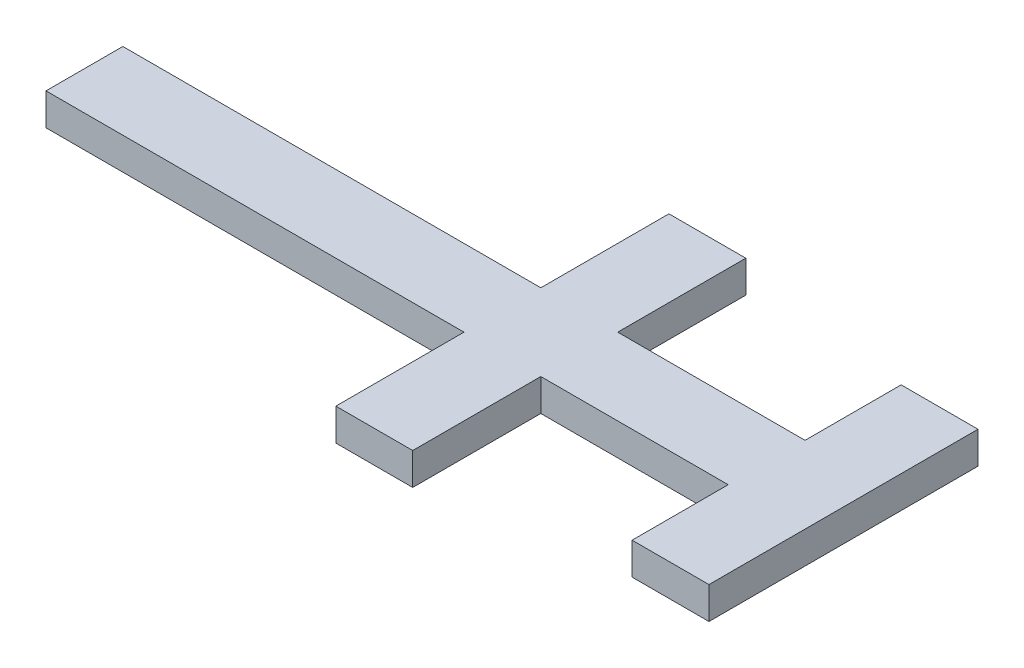
SolidWorks part; units mm, degrees
ref_plane "前视基准面" through (0, 0, 0) normal (0, 0, 1) x (1, 0, 0)
ref_plane "上视基准面" through (0, 0, 0) normal (0, 1, 0) x (1, 0, 0)
ref_plane "右视基准面" through (0, 0, 0) normal (1, 0, 0) x (0, 0, -1)
other "Configuration Table"
sketch "草图2" plane through (0, 0, 0) normal (0, 1, 0) x (1, 0, 0)
  line L0 (0, 0) -> (-46, 0) construction
  line L5 (-15.5, -5) -> (15.5, -5)
  line L6 (-15.5, -5) -> (-15.5, 5)
  line L7 (-15.5, 5) -> (15.5, 5)
  line L8 (15.5, -5) -> (15.5, 5)
  line L9 (-15.5, -5) -> (15.5, 5) construction
  line L10 (-15.5, 5) -> (15.5, -5) construction
  line L11 (20.5, 0) -> (15.5, 0) construction
  line L12 (-26, -5) -> (-66, -5)
  line L13 (-26, -5) -> (-26, 5)
  line L14 (-26, 5) -> (-66, 5)
  line L15 (-66, -5) -> (-66, 5)
  line L16 (-26, -5) -> (-66, 5) construction
  line L17 (-26, 5) -> (-66, -5) construction
  line L18 (-15.75, -25) -> (-25.75, -25)
  line L19 (-15.75, -25) -> (-15.75, 25)
  line L20 (-15.75, 25) -> (-25.75, 25)
  line L21 (-25.75, -25) -> (-25.75, 25)
  line L22 (-15.75, -25) -> (-25.75, 25) construction
  line L23 (-15.75, 25) -> (-25.75, -25) construction
  line L24 (25.5, -20) -> (15.5, -20)
  line L25 (25.5, -20) -> (25.5, 20)
  line L26 (25.5, 20) -> (15.5, 20)
  line L27 (15.5, -20) -> (15.5, 20)
  line L28 (25.5, -20) -> (15.5, 20) construction
  line L29 (25.5, 20) -> (15.5, -20) construction
  line L31 (-66, 5) -> (-91, 5)
  line L32 (-66, 5) -> (-66, -5)
  line L33 (-66, -5) -> (-91, -5)
  line L34 (-91, 5) -> (-91, -5)
  line L35 (-15.5, 5) -> (-26, 5)
  line L36 (-15.5, 5) -> (-15.5, -5)
  line L37 (-15.5, -5) -> (-26, -5)
  line L38 (-26, 5) -> (-26, -5)
  point P0 (0, 0)
  point P13 (20.5, 0)
  point P15 (-20.75, 0)
  dimension "D1" = 10
  dimension "D2" = 31
  dimension "D3" = 40
  dimension "D5" = 46
  dimension "D6" = 10
  dimension "D7" = 5.25
  dimension "D8" = 50
  dimension "D9" = 10
  dimension "D10" = 5
  dimension "D11" = 40
  dimension "D12" = 25
sketch "草图3" plane through (0, 0, 0) normal (0, 1, 0) x (1, 0, 0)
  line L0 (-15.5, -5) -> (15.5, -5) construction
  line L1 (25.5, 20) -> (15.5, 20)
  line L2 (25.5, 20) -> (25.5, -20)
  line L3 (25.5, -20) -> (15.5, -20)
  line L4 (15.5, 20) -> (15.5, -20)
  line L5 (15.5, 5) -> (-15.75, 5)
  line L6 (15.5, 5) -> (15.5, -5)
  line L7 (15.5, -5) -> (-15.75, -5)
  line L8 (-15.75, 5) -> (-15.75, -5)
  line L9 (-15.75, -25) -> (-15.75, 25) construction
  line L10 (-26, 5) -> (-66, 5) construction
  line L11 (-15.75, 25) -> (-25.75, 25)
  line L12 (-15.75, 25) -> (-15.75, -25)
  line L13 (-15.75, -25) -> (-25.75, -25)
  line L14 (-25.75, 25) -> (-25.75, -25)
  line L15 (-66, -5) -> (-25.75, -5)
  line L16 (-66, -5) -> (-66, 5)
  line L17 (-66, 5) -> (-25.75, 5)
  line L18 (-25.75, -5) -> (-25.75, 5)
  line L20 (-66, 5) -> (-91, 5)
  line L21 (-66, 5) -> (-66, -5)
  line L22 (-66, -5) -> (-91, -5)
  line L23 (-91, 5) -> (-91, -5)
extrude "凸台-拉伸1" add sketch "草图3" along normal blind 1 contours L1 L4 L3 L2 | L5 L8 L7 L4 | L11 L14 L13 L12 L8 | L17 L16 L15 L14 | L20 L23 L22 L16
sketch "草图4" plane through (0, 0, 0) normal (0, -1, 0) x (1, 0, 0)
  line L0 (14.5, -21) -> (26.5, -21)
  line L1 (26.5, -21) -> (26.5, 21)
  line L2 (26.5, 21) -> (14.5, 21)
  line L3 (14.5, 21) -> (14.5, 6)
  line L4 (14.5, 6) -> (-14.75, 6)
  line L5 (-14.75, 6) -> (-14.75, 26)
  line L6 (-14.75, 26) -> (-26.75, 26)
  line L7 (-26.75, 26) -> (-26.75, 6)
  line L8 (-26.75, 6) -> (-92, 6)
  line L9 (-92, 6) -> (-92, -6)
  line L10 (-92, -6) -> (-26.75, -6)
  line L11 (-26.75, -6) -> (-26.75, -26)
  line L12 (-26.75, -26) -> (-14.75, -26)
  line L13 (-14.75, -26) -> (-14.75, -6)
  line L14 (-14.75, -6) -> (14.5, -6)
  line L15 (14.5, -6) -> (14.5, -21)
  line L16 (15.5, -20) -> (25.5, -20)
  line L17 (25.5, -20) -> (25.5, 20)
  line L18 (25.5, 20) -> (15.5, 20)
  line L19 (15.5, 20) -> (15.5, 5)
  line L20 (15.5, 5) -> (-15.75, 5)
  line L21 (-15.75, 5) -> (-15.75, 25)
  line L22 (-15.75, 25) -> (-25.75, 25)
  line L23 (-25.75, 25) -> (-25.75, 5)
  line L24 (-25.75, 5) -> (-91, 5)
  line L25 (-91, 5) -> (-91, -5)
  line L26 (-91, -5) -> (-25.75, -5)
  line L27 (-25.75, -5) -> (-25.75, -25)
  line L28 (-25.75, -25) -> (-15.75, -25)
  line L29 (-15.75, -25) -> (-15.75, -5)
  line L30 (-15.75, -5) -> (15.5, -5)
  line L31 (15.5, -5) -> (15.5, -20)
  line L32 (15.5, -20) -> (25.5, -20)
  line L33 (25.5, -20) -> (25.5, 20)
  line L34 (25.5, 20) -> (15.5, 20)
  line L35 (15.5, 20) -> (15.5, 5)
  line L36 (15.5, 5) -> (-15.75, 5)
  line L37 (-15.75, 5) -> (-15.75, 25)
  line L38 (-15.75, 25) -> (-25.75, 25)
  line L39 (-25.75, 25) -> (-25.75, 5)
  line L40 (-25.75, 5) -> (-91, 5)
  line L41 (-91, 5) -> (-91, -5)
  line L42 (-91, -5) -> (-25.75, -5)
  line L43 (-25.75, -5) -> (-25.75, -25)
  line L44 (-25.75, -25) -> (-15.75, -25)
  line L45 (-15.75, -25) -> (-15.75, -5)
  line L46 (-15.75, -5) -> (15.5, -5)
  line L47 (15.5, -5) -> (15.5, -20)
  dimension "D1" = 0
  dimension "D2" = 1
extrude "凸台-拉伸2" add sketch "草图4" along normal blind 4 and the other way blind 1
sketch "草图5" plane through (0, 0, 0) normal (0, -1, 0) x (1, 0, 0)
  line L0 (-25.75, 25) -> (-25.75, 5)
  line L1 (-91, 5) -> (-66, 5)
  line L2 (-91, 5) -> (-91, -5)
  line L3 (-91, -5) -> (-66, -5)
  line L4 (-66, 5) -> (-66, -5)
  line L5 (15.5, 20) -> (25.5, 20)
  line L6 (15.5, 20) -> (15.5, -20)
  line L7 (15.5, -20) -> (25.5, -20)
  line L8 (25.5, 20) -> (25.5, -20)
  line L9 (-25.75, 5) -> (-26, 5)
  line L10 (-26, 5) -> (-26, -5)
  line L11 (-26, -5) -> (-25.75, -5)
  line L12 (-25.75, -5) -> (-25.75, -25)
  line L13 (-25.75, -25) -> (-15.75, -25)
  line L14 (-15.75, -25) -> (-15.75, -5)
  line L15 (-15.75, -5) -> (-15.5, -5)
  line L16 (-15.5, -5) -> (-15.5, 5)
  line L17 (-15.5, 5) -> (-15.75, 5)
  line L18 (-15.75, 5) -> (-15.75, 25)
  line L19 (-15.75, 25) -> (-25.75, 25)
extrude "凸台-拉伸3" add sketch "草图5" along normal blind 2
